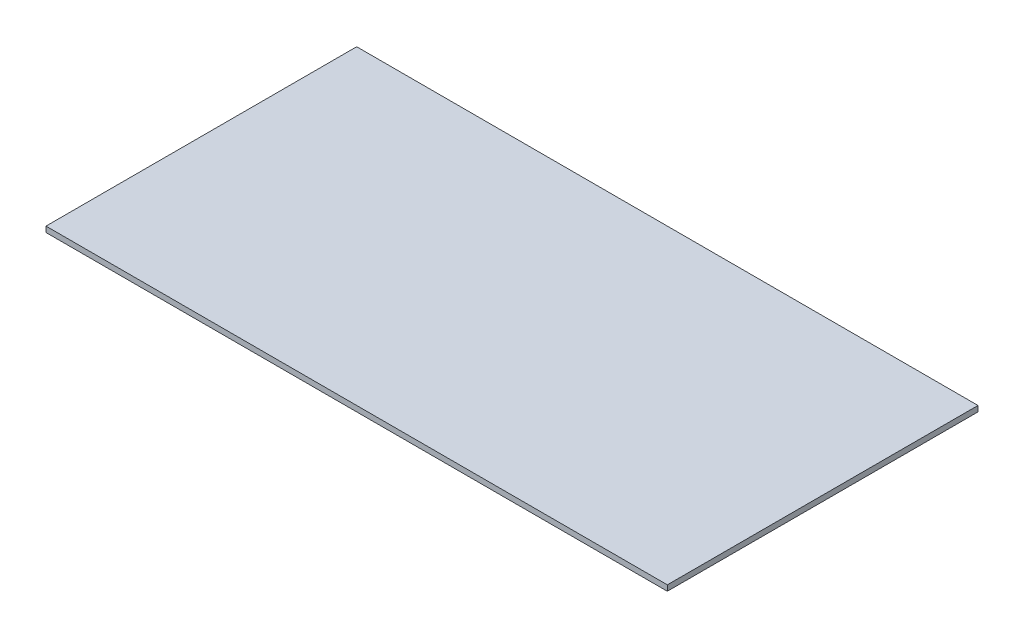
SolidWorks part; units mm, degrees
ref_plane "Front Plane" through (0, 0, 0) normal (0, 0, 1) x (1, 0, 0)
ref_plane "Top Plane" through (0, 0, 0) normal (0, 1, 0) x (1, 0, 0)
ref_plane "Right Plane" through (0, 0, 0) normal (1, 0, 0) x (0, 0, -1)
sketch "Sketch1" plane through (0, 0, 0) normal (0, 1, 0) x (1, 0, 0)
  line L1 (0, 0) -> (50, 0)
  line L2 (0, 0) -> (0, 25)
  line L3 (0, 25) -> (50, 25)
  line L4 (50, 0) -> (50, 25)
  dimension "D1" = 50
  dimension "D2" = 25
extrude "Boss-Extrude1" add sketch "Sketch1" along normal blind 0.45
